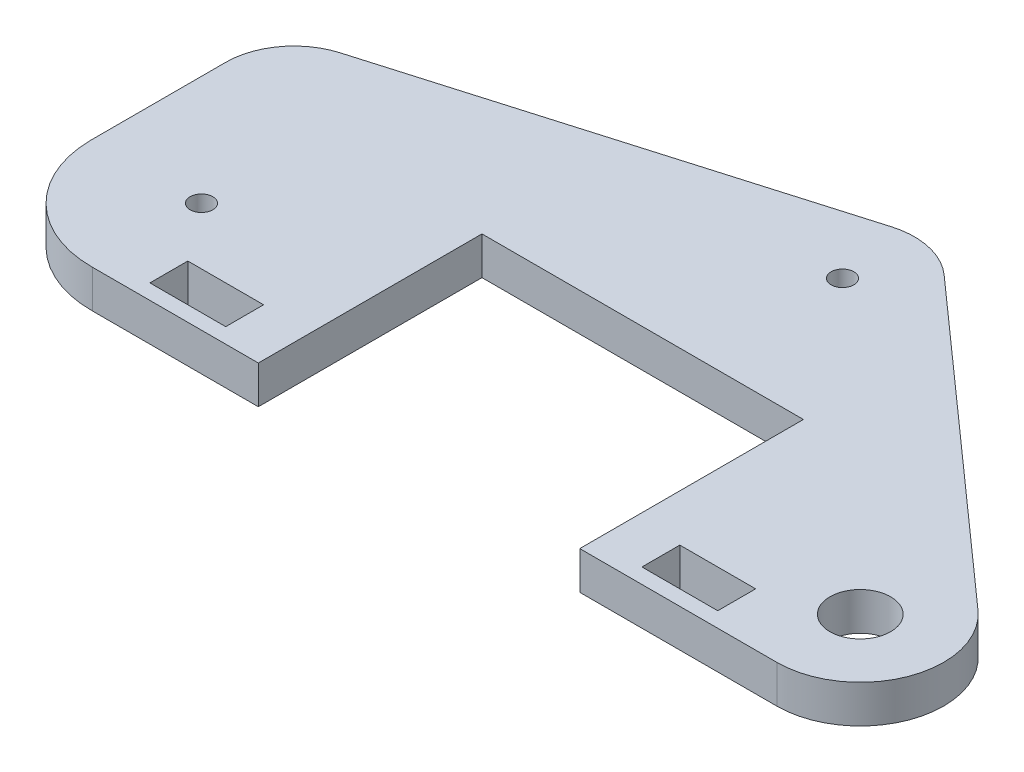
SolidWorks part; units mm, degrees
ref_plane "Front Plane" through (0, 0, 0) normal (0, 0, 1) x (1, 0, 0)
ref_plane "Top Plane" through (0, 0, 0) normal (0, 1, 0) x (1, 0, 0)
ref_plane "Right Plane" through (0, 0, 0) normal (1, 0, 0) x (0, 0, -1)
sketch "Sketch1" plane through (0, 0, 0) normal (0, 1, 0) x (1, 0, 0)
  line L0 (0, 0) -> (0, 1.5) construction
  line L1 (0.1028, -14.4996) -> (22.0028, -14.4996)
  line L2 (22.0028, -14.4996) -> (22.0028, 15.0004)
  line L3 (22.0028, 15.0004) -> (64.4028, 15.0004)
  line L4 (64.4028, 15.0004) -> (64.4028, -14.4996)
  line L5 (64.4028, -14.4996) -> (90.4028, -14.4996)
  line L6 (-14.4996, -0.1028) -> (-14.4996, 17.6972)
  line L7 (57.1686, 40.7971) -> (97.7151, 4.7181)
  line L10 (5.7, -12.4996) -> (5.7, -7.4996)
  line L11 (-8.032, 26.3335) -> (48.1804, 42.8162)
  line L12 (80.6028, -12.4996) -> (80.6028, -7.4996)
  line L13 (5.7, -7.4996) -> (15.7, -7.4996)
  line L14 (15.7, -7.4996) -> (15.7, -12.4996)
  line L15 (15.7, -12.4996) -> (5.7, -12.4996)
  line L17 (80.6028, -7.4996) -> (70.6028, -7.4996)
  line L18 (70.6028, -7.4996) -> (70.6028, -12.4996)
  line L19 (70.6028, -12.4996) -> (80.6028, -12.4996)
  circle A0 centre (0, 0) radius 1.5
  arc A1 (-14.4996, -0.1028) -> (0.1028, -14.4996) centre (0, 0) ccw
  arc A2 (-8.032, 26.3335) -> (-14.4996, 17.6972) centre (-5.4996, 17.6972) ccw
  arc A3 (90.4028, -14.4996) -> (97.7151, 4.7181) centre (90.4028, -3.4996) ccw
  circle A4 centre (90.4028, -3.4996) radius 4
  circle A5 centre (50.8534, 33.7) radius 1.5
  arc A6 (57.1686, 40.7971) -> (48.1804, 42.8162) centre (50.8534, 33.7) ccw
  dimension "D1" = 3
  dimension "D2" = 90
  dimension "D3" = 14.5
  dimension "D12" = 18
  dimension "D13" = 22
  dimension "D14" = 19
  dimension "D15" = 54.2745
  dimension "D17" = 8
  dimension "D19" = 3
  dimension "D20" = 6.3028
  dimension "D16" = 33.7
  dimension "D4" = 7.4996
  dimension "D5" = 14.4996
  dimension "D6" = 21.9
  dimension "D7" = 29.5
  dimension "D8" = 42.4
  dimension "D9" = 29.5
  dimension "D10" = 26
  dimension "D11" = 17.8
  dimension "D18" = 58.5791
  dimension "D22" = 39.5494
  dimension "D23" = 5
  dimension "D24" = 10
  dimension "D25" = 5
  dimension "D26" = 9.8
  dimension "D28" = 5
  dimension "D29" = 10
  dimension "D30" = 5
  dimension "D31" = 4
extrude "Boss-Extrude1" add sketch "Sketch1" along normal blind 5
